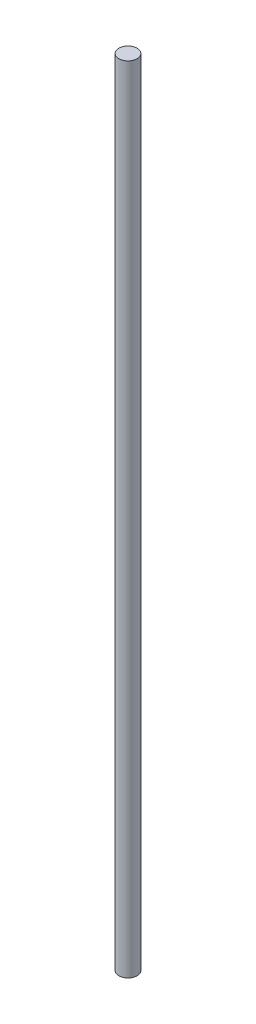
SolidWorks part; units mm, degrees
ref_plane "Front Plane" through (0, 0, 0) normal (0, 0, 1) x (1, 0, 0)
ref_plane "Top Plane" through (0, 0, 0) normal (0, 1, 0) x (1, 0, 0)
ref_plane "Right Plane" through (0, 0, 0) normal (1, 0, 0) x (0, 0, -1)
sketch "Sketch1" plane through (0, 0, 0) normal (0, 1, 0) x (1, 0, 0)
  circle A0 centre (0, 0) radius 1.75
  dimension "D1" = 3.5
extrude "Boss-Extrude1" add sketch "Sketch1" along normal blind 152.4
